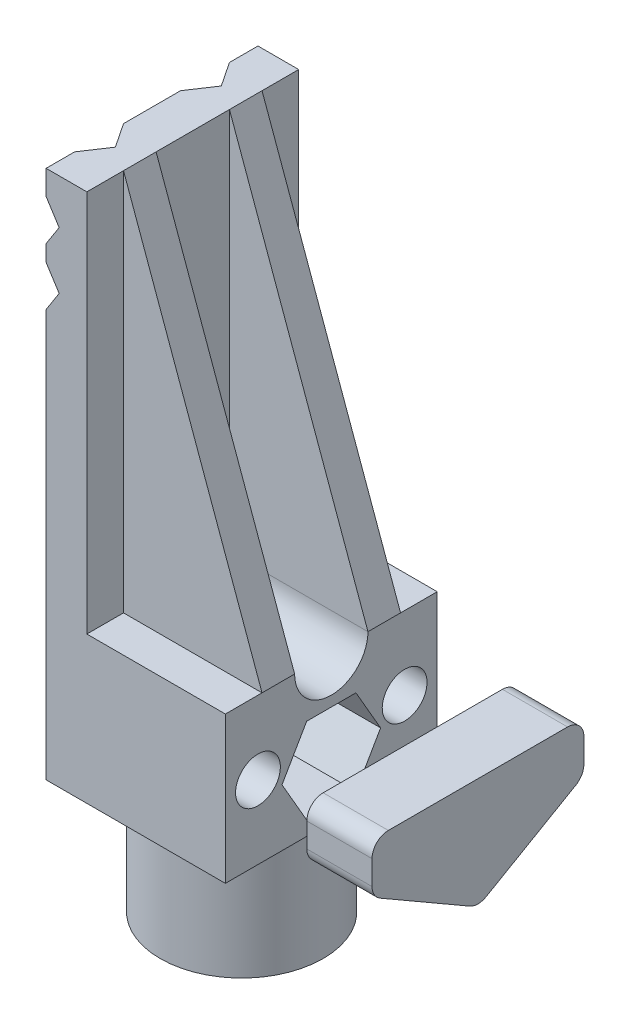
SolidWorks part; units mm, degrees
ref_plane "Alzado" through (0, 0, 0) normal (0, 0, 1) x (1, 0, 0)
ref_plane "Planta" through (0, 0, 0) normal (0, 1, 0) x (1, 0, 0)
ref_plane "Vista lateral" through (0, 0, 0) normal (1, 0, 0) x (0, 0, -1)
sketch "Croquis1" plane through (0, 0, 0) normal (0, 0, 1) x (1, 0, 0)
  line L0 (-24.8099, 23.3973) -> (-24.8099, 21.3973)
  line L1 (-24.8099, -33.6027) -> (-2.8099, -33.6027)
  line L2 (-2.8099, -33.6027) -> (-2.8099, -15.6027)
  line L3 (-2.8099, -15.6027) -> (-19.8099, -15.6027)
  line L4 (-19.8099, -15.6027) -> (-19.8099, 31.3973)
  line L5 (-19.8099, 31.3973) -> (-24.8099, 31.3973)
  line L6 (-24.8099, 31.3973) -> (-24.8099, 28.3973)
  line L7 (-24.8099, 28.3973) -> (-23.2099, 25.8973)
  line L8 (-23.2099, 25.8973) -> (-24.8099, 23.3973)
  line L9 (-18.7986, 22.3973) -> (-31.0641, 22.3973) construction
  line L10 (-23.2099, 18.8973) -> (-24.8099, 21.3973)
  line L11 (-24.8099, 16.3973) -> (-23.2099, 18.8973)
  line L12 (-24.8099, 16.3973) -> (-24.8099, -33.6027)
  point P11 (-24.0099, 24.6473)
  point P14 (-24.0099, 20.1473)
  dimension "D1" = 65
  dimension "D2" = 5
  dimension "D3" = 18
  dimension "D4" = 22
  dimension "D5" = 3
  dimension "D6" = 5
  dimension "D7" = 1.6
  dimension "D8" = 2
extrude "Saliente-Extruir1" add sketch "Croquis1" along normal blind 26
sketch "Croquis7" plane through (-19.8099, 0, 0) normal (1, 0, 0) x (0, 0, -1)
  line L0 (-13, 31.3973) -> (-13, -15.6027) construction
  line L1 (-26, 31.3973) -> (0, 31.3973) construction
  line L2 (-26, -15.6027) -> (0, -15.6027) construction
  line L3 (-26, 31.3973) -> (-13, -15.6027) construction
  line L4 (-13, 31.3973) -> (-26, -15.6027) construction
  line L7 (-26, -15.6027) -> (0, -15.6027) construction
  line L8 (-19.5, -15.6027) -> (-19.5, 31.3973) construction
ref_plane "Plano1" through (0, 0, 19.5) normal (0, 0, -1) x (-1, 0, 0)
sketch "Croquis15" plane through (-2.8099, 0, 0) normal (1, 0, 0) x (0, 0, -1)
  line L0 (-26, -33.6027) -> (0, -33.6027) construction
  circle A0 centre (-13, -26.6027) radius 3.25
  point P4 (-13, -33.6027)
  dimension "D1" = 6.5
  dimension "D2" = 7
extrude "Cortar-Extruir5" cut sketch "Croquis15" against normal blind 28
sketch "Croquis8" plane through (0, 0, 19.5) normal (0, 0, -1) x (-1, 0, 0)
  line L0 (19.8099, 31.3973) -> (19.8099, -15.6027)
  line L1 (19.8099, -15.6027) -> (2.8099, -15.6027)
  line L2 (2.8099, -15.6027) -> (19.8099, 31.3973)
extrude "Saliente-Extruir3" add sketch "Croquis8" against normal blind 2 and the other way blind 2
ref_plane "Plano2" through (0, 0, 13) normal (0, 0, -1) x (-1, 0, 0)
mirror "Simetría1" about plane through (0, 0, 13) normal (0, 0, -1) of "Saliente-Extruir3"
sketch "Croquis9" plane through (-2.8099, 0, 0) normal (1, 0, 0) x (0, 0, -1)
  line L0 (-17.5, -15.6027) -> (-8.5, -15.6027) construction
  circle A0 centre (-13, -15.6027) radius 4.5
extrude "Cortar-Extruir1" cut sketch "Croquis9" against normal blind 17
sketch "Croquis10" plane through (-2.8099, 0, 0) normal (1, 0, 0) x (0, 0, -1)
  line L0 (-26, -15.6027) -> (0, -33.6027) construction
  line L1 (-26, -33.6027) -> (0, -15.6027) construction
  line L2 (-26, -24.6027) -> (0, -24.6027) construction
  line L3 (-26, -33.6027) -> (-26, -15.6027) construction
  line L4 (0, -33.6027) -> (0, -15.6027) construction
  line L5 (-13, -19.402) -> (-13, -33.6027) construction
  line L6 (-13, -9.35) -> (-13, 9.35) construction
  line L7 (-26, -33.6027) -> (0, -33.6027) construction
  circle A0 centre (-22, -24.6027) radius 2.75
  circle A1 centre (-4, -24.6027) radius 2.75
  point P25 (-13, -26.5023)
  dimension "D1" = 5.5
  dimension "D2" = 4
  dimension "D3" = 9
  dimension "D4" = 4
  dimension "D5" = 1.8997
extrude "Cortar-Extruir2" cut sketch "Croquis10" against normal blind 22
sketch "Croquis12" plane through (0, 31.3973, 0) normal (0, 1, 0) x (1, 0, 0)
  line L0 (-24.8099, -22.5) -> (-24.8099, -16.5)
  line L1 (-24.8099, -26) -> (-24.8099, 0) construction
  line L2 (-24.8099, -16.5) -> (-22.8099, -19.5)
  line L3 (-22.8099, -19.5) -> (-24.8099, -22.5)
  line L4 (-19.8099, -13) -> (-24.8099, -13) construction
  line L5 (-19.8099, -17.5) -> (-19.8099, -8.5) construction
  line L6 (-22.8099, -6.5) -> (-24.8099, -3.5)
  line L7 (-24.8099, -9.5) -> (-22.8099, -6.5)
  line L8 (-24.8099, -3.5) -> (-24.8099, -9.5)
  dimension "D1" = 6
  dimension "D2" = 2
  dimension "D3" = 3.5
extrude "Cortar-Extruir3" cut sketch "Croquis12" against normal blind 50
ref_plane "Plano4" through (7.1901, 0, 0) normal (1, 0, 0) x (0, 0, -1)
sketch "Croquis17" plane through (7.1901, 0, 0) normal (1, 0, 0) x (0, 0, -1)
  line L0 (-26, -33.6027) -> (-26, -15.6027) construction
  line L1 (-26, -19.9761) -> (0, -19.9761)
  line L2 (0, -19.9761) -> (0, -26.0994)
  line L3 (0, -33.6027) -> (0, -15.6027) construction
  line L4 (0, -26.0994) -> (-13, -33.6027)
  line L5 (-26, -33.6027) -> (0, -33.6027) construction
  line L6 (-13, -33.6027) -> (-26, -26.0994)
  line L7 (-26, -26.0994) -> (-26, -19.9761)
extrude "Saliente-Extruir5" add sketch "Croquis17" along normal blind 8 separate body
fillet "Redondeo2" radius 2 1 edges at (11.1901, -33.6027, 13)
fillet "Redondeo3" radius 2 4 edges at (11.1901, -19.9761, 0) (11.1901, -19.9761, 26) (11.1901, -26.0994, 26) (11.1901, -26.0994, 0)
sketch "Croquis18" plane through (7.1901, 0, 0) normal (1, 0, 0) x (0, 0, -1)
  line L0 (-26, -33.6027) -> (0, -33.6027) construction
  line L1 (-26, -21.9761) -> (-26, -24.9445) construction
  line L2 (0, -24.9445) -> (0, -21.9761) construction
  circle A0 centre (-22, -24.6027) radius 2.7
  circle A1 centre (-13, -26.6027) radius 3.2
  circle A2 centre (-4, -24.6027) radius 2.7
  point P18 (-13, -33.6027)
  dimension "D1" = 5.4
  dimension "D2" = 5.4
  dimension "D3" = 6.4
  dimension "D4" = 18
  dimension "D5" = 2
  dimension "D6" = 7
  dimension "D7" = 9
  dimension "D8" = 7
  dimension "D9" = 4
  dimension "D10" = 4
  dimension "D11" = 9
extrude "Cortar-Extruir6" cut sketch "Croquis18" along normal blind 6
sketch "Croquis19" plane through (0, -33.6027, 0) normal (0, -1, 0) x (1, 0, 0)
  line L0 (-9.35, 13) -> (9.35, 13) construction
  line L1 (-24.8099, 26) -> (-2.8099, 0) construction
  line L2 (-24.8099, 0) -> (-2.8099, 26) construction
  circle A0 centre (-13.8099, 13) radius 10
  circle A1 centre (-13.8099, 13) radius 3
  dimension "D1" = 20
  dimension "D2" = 6
extrude "Saliente-Extruir6" add sketch "Croquis19" along normal blind 15
ref_plane "Plano6" through (-2.8099, 0, 0) normal (1, 0, 0) x (0, 0, -1)
sketch "Croquis21" plane through (-2.8099, 0, 0) normal (1, 0, 0) x (0, 0, -1)
  line L1 (-9.975, -21.3632) -> (-16.025, -21.3632)
  line L2 (-16.025, -21.3632) -> (-19.05, -26.6027)
  line L3 (-19.05, -26.6027) -> (-16.025, -31.8421)
  line L4 (-16.025, -31.8421) -> (-9.975, -31.8421)
  line L5 (-9.975, -31.8421) -> (-6.95, -26.6027)
  line L6 (-6.95, -26.6027) -> (-9.975, -21.3632)
  circle A0 centre (-13, -26.6027) radius 5.2395 construction
  dimension "D1" = 6.05
extrude "Cortar-Extruir7" cut sketch "Croquis21" against normal blind 10
